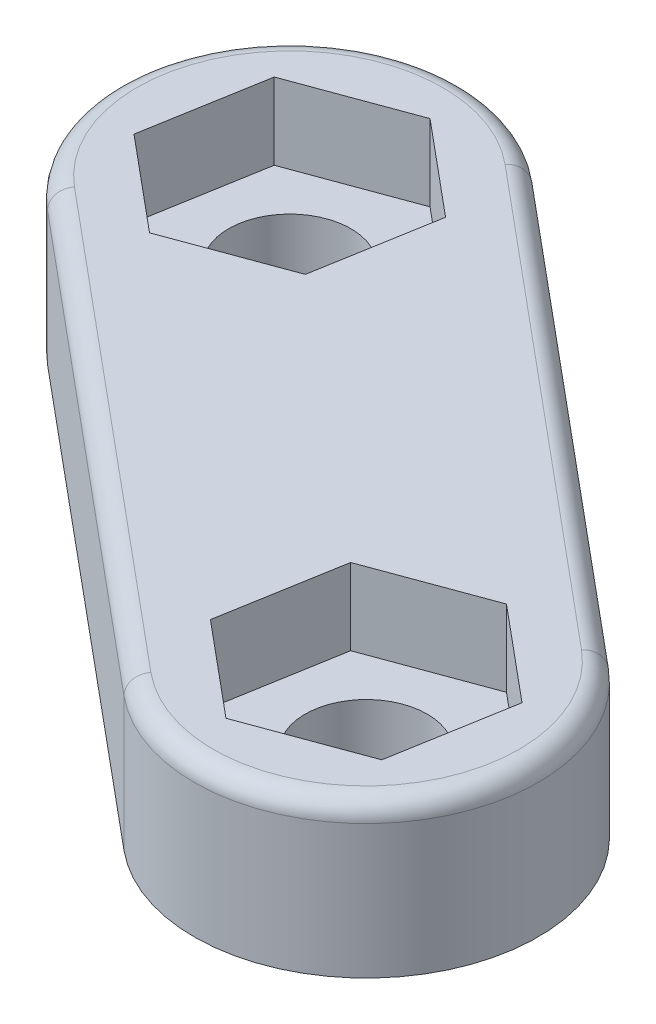
SolidWorks part; units mm, degrees
ref_plane "Front Plane" through (0, 0, 0) normal (0, 0, 1) x (1, 0, 0)
ref_plane "Top Plane" through (0, 0, 0) normal (0, 1, 0) x (1, 0, 0)
ref_plane "Right Plane" through (0, 0, 0) normal (1, 0, 0) x (0, 0, -1)
sketch "Sketch1" plane through (0, 0, 0) normal (0, 1, 0) x (1, 0, 0)
  line L0 (-8.8808, 1.543) -> (3.1192, -8.457)
  line L1 (-6, 5) -> (6, 5)
  line L2 (-6, 5) -> (-6, -5)
  line L3 (-6, -5) -> (6, -5)
  line L4 (6, 5) -> (6, -5)
  line L5 (-6, 5) -> (6, -5) construction
  line L6 (-6, -5) -> (6, 5) construction
  line L7 (-3.1192, 8.457) -> (8.8808, -1.543)
  circle A0 centre (-6, 5) radius 4.5
  circle A1 centre (6, -5) radius 4.5
  circle A2 centre (-6, 5) radius 1.6
  circle A3 centre (6, -5) radius 1.6
  point P0 (0, 0)
  dimension "D3" = 9
  dimension "D4" = 3.2
  dimension "D1" = 12
  dimension "D2" = 10
extrude "Boss-Extrude1" add sketch "Sketch1" along normal blind 4 contours A2 L1 A0 L2 | A2 L2 A0 L1 | A1 L4 L7 L1 A0 L2 L0 L3 | A3 L4 A1 L3 | A3 L3 A1 L4 | A1 L3 L0 | A0 L0 L2 | A1 L7 L4 | A0 L1 L7
sketch "Sketch2" plane through (0, 4, 0) normal (0, 1, 0) x (1, 0, 0)
  line L0 (-8.8808, 1.543) -> (3.1192, -8.457) construction
  line L1 (-8.4394, 7.0329) -> (-8.9802, 3.9038)
  line L2 (-8.9802, 3.9038) -> (-6.5408, 1.871)
  line L3 (-6.5408, 1.871) -> (-3.5606, 2.9671)
  line L4 (-3.5606, 2.9671) -> (-3.0198, 6.0962)
  line L5 (-3.0198, 6.0962) -> (-5.4592, 8.129)
  line L6 (-5.4592, 8.129) -> (-8.4394, 7.0329)
  line L7 (2.8808, 3.457) -> (-2.8808, -3.457) construction
  line L8 (-3.1192, 8.457) -> (8.8808, -1.543) construction
  line L9 (5.4592, -8.129) -> (3.0198, -6.0962)
  line L10 (8.4394, -7.0329) -> (5.4592, -8.129)
  line L11 (8.9802, -3.9038) -> (8.4394, -7.0329)
  line L12 (6.5408, -1.871) -> (8.9802, -3.9038)
  line L13 (3.5606, -2.9671) -> (6.5408, -1.871)
  line L14 (3.0198, -6.0962) -> (3.5606, -2.9671)
  circle A0 centre (-6, 5) radius 2.75 construction
  dimension "D1" = 5.5
extrude "Cut-Extrude1" cut sketch "Sketch2" against normal blind 2
fillet "Fillet1" radius 0.5 4 edges at (-9.457, 4, -7.8808) (2.8808, 4, -3.457) (9.457, 4, 7.8808) (-2.8808, 4, 3.457)
